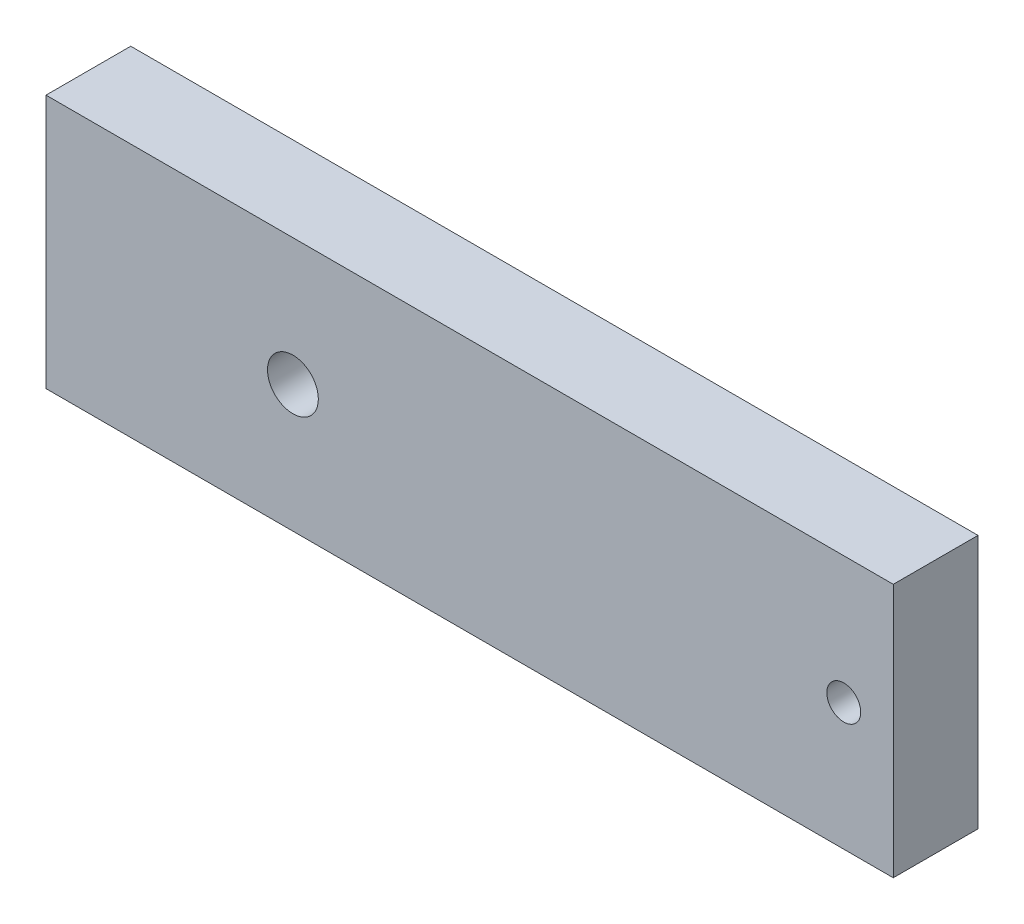
SolidWorks part; units mm, degrees
ref_plane "Front Plane" through (0, 0, 0) normal (0, 0, 1) x (1, 0, 0)
ref_plane "Top Plane" through (0, 0, 0) normal (0, 1, 0) x (1, 0, 0)
ref_plane "Right Plane" through (0, 0, 0) normal (1, 0, 0) x (0, 0, -1)
sketch "Sketch2" plane through (0, 0, 0) normal (0, 0, 1) x (1, 0, 0)
  line L1 (-25, -7.5) -> (25, -7.5)
  line L2 (-25, -7.5) -> (-25, 7.5)
  line L3 (-25, 7.5) -> (25, 7.5)
  line L4 (25, -7.5) -> (25, 7.5)
  line L5 (-25, -7.5) -> (25, 7.5) construction
  line L6 (-25, 7.5) -> (25, -7.5) construction
  point P0 (0, 0)
  dimension "D1" = 50
  dimension "D2" = 15
extrude "Boss-Extrude1" add sketch "Sketch2" along normal blind 5
sketch "Sketch3" plane through (0, 0, 5) normal (0, 0, 1) x (1, 0, 0)
  circle A0 centre (-10.4292, 0) radius 1.5
  dimension "D1" = 3
extrude "Cut-Extrude1" cut sketch "Sketch3" against normal through all
sketch "Sketch4" plane through (0, 0, 5) normal (0, 0, 1) x (1, 0, 0)
  circle A0 centre (22.0789, 0) radius 1
extrude "Cut-Extrude2" cut sketch "Sketch4" against normal through all
